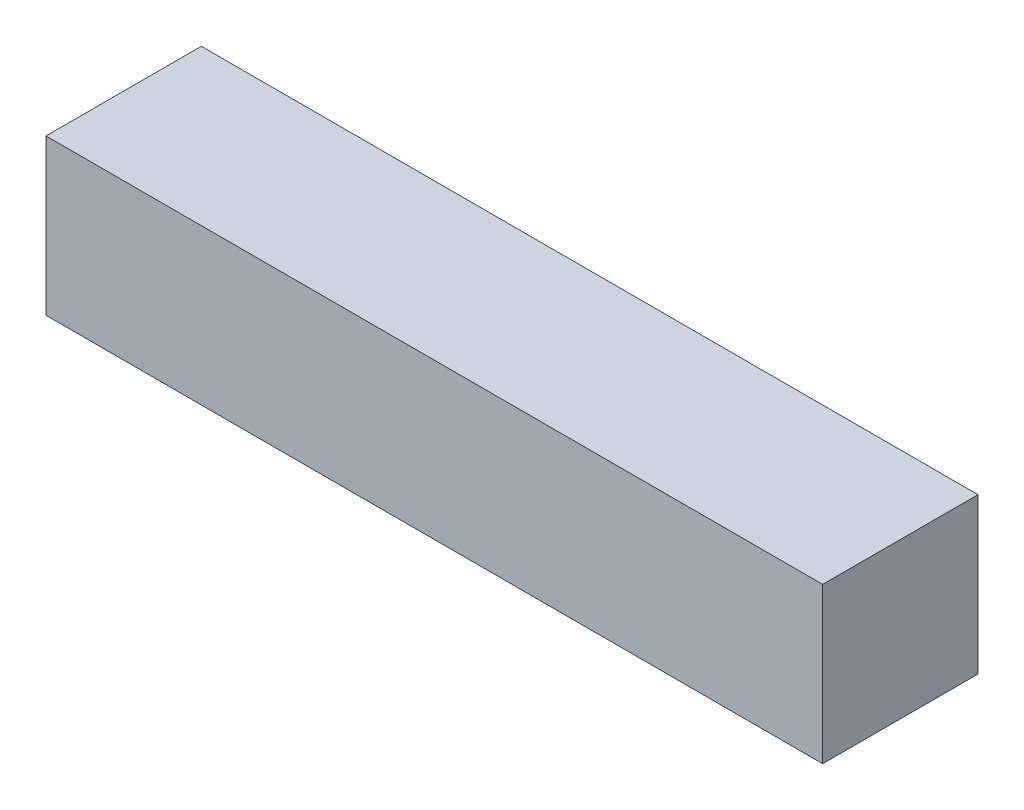
SolidWorks part; units mm, degrees
ref_plane "Front Plane" through (0, 0, 0) normal (0, 0, 1) x (1, 0, 0)
ref_plane "Top Plane" through (0, 0, 0) normal (0, 1, 0) x (1, 0, 0)
ref_plane "Right Plane" through (0, 0, 0) normal (1, 0, 0) x (0, 0, -1)
sketch "Sketch1" plane through (0, 0, 0) normal (0, 0, 1) x (1, 0, 0)
  line L32 (0, 0) -> (0, 25.4)
  line L33 (0, 25.4) -> (127, 25.4)
  line L34 (127, 25.4) -> (127, 0)
  line L35 (127, 0) -> (0, 0)
extrude "Boss-Extrude1" add sketch "Sketch1" along normal blind 25.4
